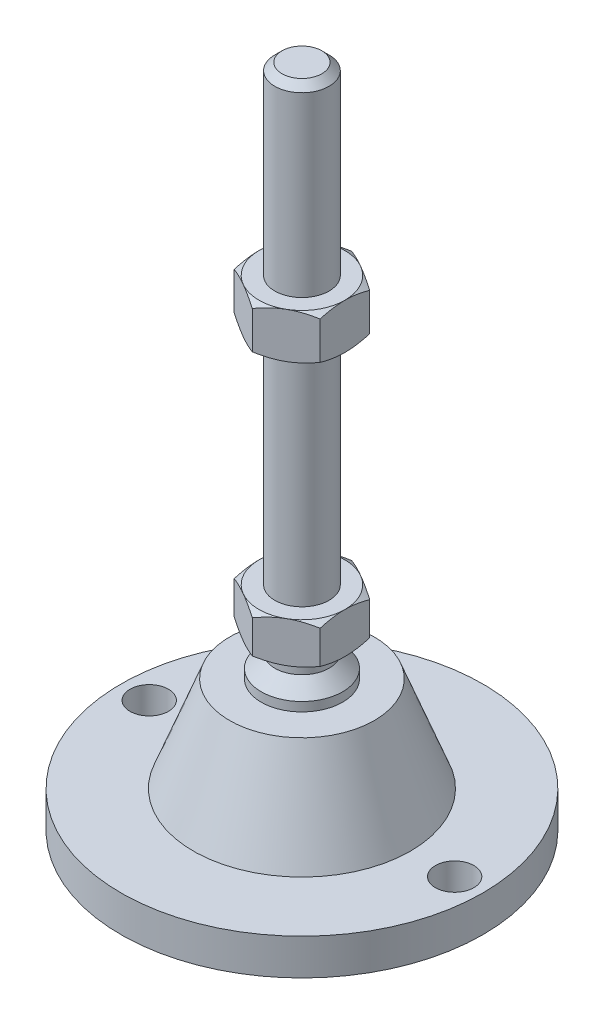
SolidWorks part; units mm, degrees
ref_plane "Спереди" through (0, 0, 0) normal (0, 0, 1) x (1, 0, 0)
ref_plane "Сверху" through (0, 0, 0) normal (0, 1, 0) x (1, 0, 0)
ref_plane "Справа" through (0, 0, 0) normal (1, 0, 0) x (0, 0, -1)
sketch "Эскиз1" plane through (0, 0, 0) normal (0, 0, 1) x (1, 0, 0)
  line L0 (0, 0) -> (-40, 0)
  line L3 (-40, 0) -> (-40, 8)
  line L12 (-6, 47) -> (-6, 145.4)
  line L13 (-6, 145.4) -> (-4.4, 147)
  line L14 (-4.4, 147) -> (0, 147)
  line L15 (0, 147) -> (0, 0) construction
  line L16 (-40, 8) -> (-24, 8)
  line L17 (0, 0) -> (0, 147)
  line L18 (0, 0) -> (0, -7.9595) construction
  line L19 (-6, 47) -> (-6, 38)
  line L21 (-9, 29) -> (-16, 29)
  line L22 (-24, 8) -> (-16, 29)
  line L23 (-9, 29) -> (-9, 31)
  line L24 (-9, 31) -> (-6, 34)
  line L25 (-6, 34) -> (-6, 38)
  line L26 (-6, 47) -> (0, 47) construction
  point P8 (-6, 96.2)
revolve "Повернуть1" add sketch "Эскиз1" angle 360 about L17
ref_plane "Плоскость2" through (0, 38, 0) normal (0, 1, 0) x (1, 0, 0)
sketch "Эскиз2" plane through (0, 38, 0) normal (0, 1, 0) x (1, 0, 0)
  line L1 (0, 10.9697) -> (-9.5, 5.4848)
  line L2 (-9.5, 5.4848) -> (-9.5, -5.4848)
  line L3 (-9.5, -5.4848) -> (0, -10.9697)
  line L4 (0, -10.9697) -> (9.5, -5.4848)
  line L5 (9.5, -5.4848) -> (9.5, 5.4848)
  line L6 (9.5, 5.4848) -> (0, 10.9697)
  circle A0 centre (0, 0) radius 9.5 construction
  dimension "D1" = 19
extrude "Бобышка-Вытянуть1" add sketch "Эскиз2" along normal up to vertex (9 mm away) up to point (-6, 47, 0)
ref_plane "Плоскость1" through (0, 96.2, 0) normal (0, 1, 0) x (1, 0, 0)
sketch "Эскиз3" plane through (0, 96.2, 0) normal (0, 1, 0) x (1, 0, 0)
  line L6 (9.5, 5.4848) -> (0, 10.9697)
  line L7 (0, 10.9697) -> (-9.5, 5.4848)
  line L8 (-9.5, 5.4848) -> (-9.5, -5.4848)
  line L9 (-9.5, -5.4848) -> (0, -10.9697)
  line L10 (0, -10.9697) -> (9.5, -5.4848)
  line L11 (9.5, -5.4848) -> (9.5, 5.4848)
  line L12 (9.5, 5.4848) -> (0, 10.9697)
  line L13 (0, 10.9697) -> (-9.5, 5.4848)
  line L14 (-9.5, 5.4848) -> (-9.5, -5.4848)
  line L15 (-9.5, -5.4848) -> (0, -10.9697)
  line L16 (0, -10.9697) -> (9.5, -5.4848)
  line L17 (9.5, -5.4848) -> (9.5, 5.4848)
  dimension "D1" = 0
extrude "Бобышка-Вытянуть2" add sketch "Эскиз3" along normal blind 10
sketch "Эскиз4" plane through (0, 0, 0) normal (0, 0, 1) x (1, 0, 0)
  line L0 (-9.5, 106.2) -> (-18.1603, 101.2)
  line L1 (-18.1603, 101.2) -> (-18.1603, 106.2)
  line L2 (-18.1603, 106.2) -> (-9.5, 106.2)
  line L3 (-18.1603, 101.2) -> (-9.5, 96.2)
  line L4 (50, 96.2) -> (-50, 96.2) construction
  line L5 (-9.5, 96.2) -> (-18.1603, 96.2)
  line L6 (-18.1603, 96.2) -> (-18.1603, 101.2)
  line L7 (-9.5, 106.2) -> (-9.5, 96.2) construction
  line L8 (-9.5, 47) -> (-17.2942, 47)
  line L9 (-17.2942, 47) -> (-17.2942, 42.5)
  line L10 (-17.2942, 42.5) -> (-9.5, 47)
  line L11 (-9.5, 38) -> (-17.2942, 42.5)
  line L12 (-17.2942, 42.5) -> (-17.2942, 38)
  line L13 (-17.2942, 38) -> (-9.5, 38)
  line L14 (0, 147) -> (0, 96.3793) construction
  line L15 (50, 38) -> (-50, 38) construction
  dimension "D1" = 30
  dimension "D2" = 30
revolve "Вырез-Повернуть2" cut sketch "Эскиз4" angle 360 about L14
sketch "Эскиз5" plane through (0, 8, 0) normal (0, 1, 0) x (1, 0, 0)
  line L0 (33.75, 0) -> (-33.75, 0) construction
  circle A0 centre (-33.75, 0) radius 4.25
  circle A1 centre (33.75, 0) radius 4.25
  circle A2 centre (0, 0) radius 40 construction
  dimension "D1" = 8.5
  dimension "D2" = 2
extrude "Вырез-Вытянуть1" cut sketch "Эскиз5" against normal through all
equation "\"D13@Эскиз1\"=\"D12@Эскиз1\"/2"
